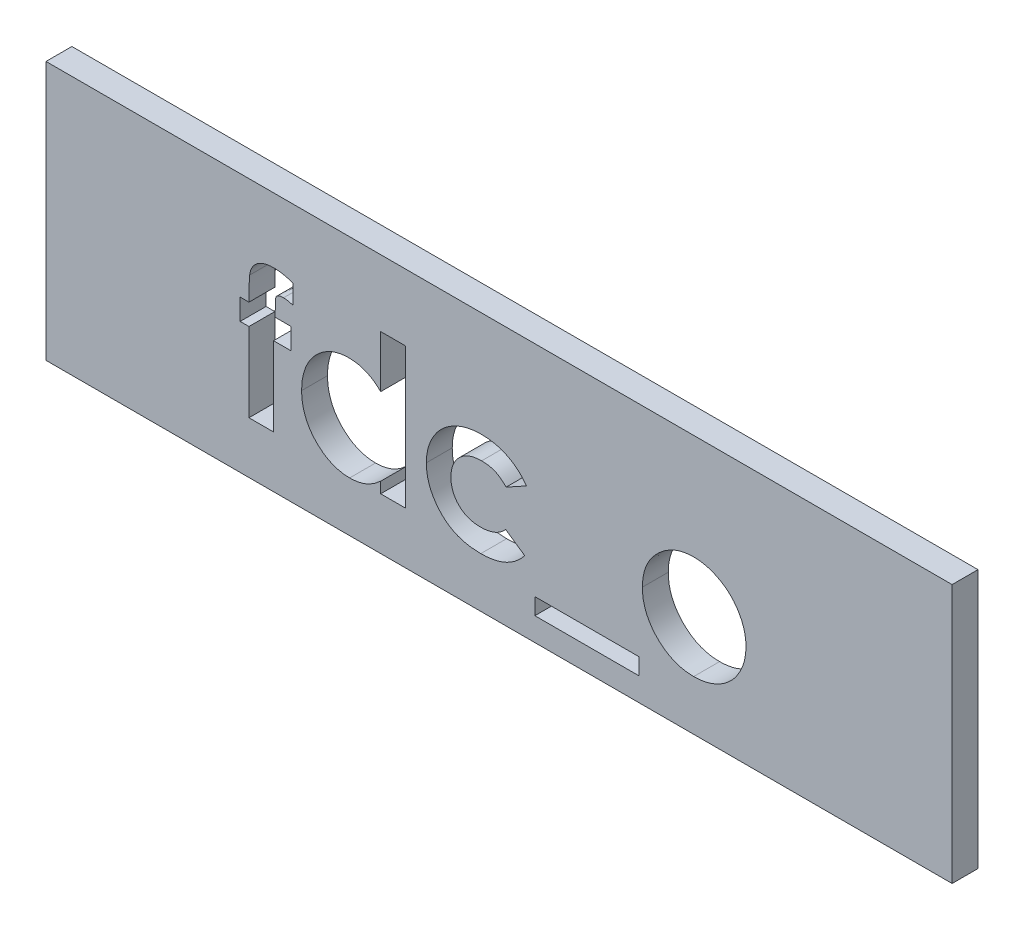
SolidWorks part; units mm, degrees
ref_plane "Plan de face" through (0, 0, 0) normal (0, 0, 1) x (1, 0, 0)
ref_plane "Plan de dessus" through (0, 0, 0) normal (0, 1, 0) x (1, 0, 0)
ref_plane "Plan de droite" through (0, 0, 0) normal (1, 0, 0) x (0, 0, -1)
sketch "Esquisse1" plane through (0, 0, 0) normal (0, 0, 1) x (1, 0, 0)
  line L1 (0, 0) -> (35, 0)
  line L2 (0, 0) -> (0, -10)
  line L3 (0, -10) -> (35, -10)
  line L4 (35, 0) -> (35, -10)
  dimension "D1" = 35
  dimension "D2" = 10
extrude "Boss.-Extru.1" add sketch "Esquisse1" along normal blind 1
sketch "Esquisse2" plane through (0, 0, 0) normal (0, 0, -1) x (-1, 0, 0)
  line L0 (-35, 0) -> (0, 0) construction
  line L1 (-35, -10) -> (-35, 0) construction
  line L2 (0, 0) -> (0, -10) construction
  circle A0 centre (-30, -5) radius 1
  circle A1 centre (-5, -5) radius 1
  dimension "D4" = 2
  dimension "D1" = 5
  dimension "D2" = 5
  dimension "D3" = 5
extrude "Boss.-Extru.2" add sketch "Esquisse2" along normal blind 3
chamfer "Chanfrein1" distance 0.5 angle 45 2 edges at (29, -5, -3) (4, -5, -3)
sketch "Esquisse3" plane through (0, 0, 1) normal (0, 0, 1) x (1, 0, 0)
  line L0 (7.5, -8) -> (27.5, -8) construction
  line L3 (0, -10) -> (35, -10) construction
  line L4 (0, 0) -> (0, -10) construction
  line L5 (35, -10) -> (35, 0) construction
  text T1 "<b>fdc_o</b>" font "Century Gothic" height in points 20
  point P12 (27.5, -8)
  dimension "D1" = 2
  dimension "D2" = 7.5
  dimension "D3" = 20
  dimension "D4" = 7.5
extrude "Enlèv. mat.-Extru.2" cut sketch "Esquisse3" against normal blind 1
sketch "Esquisse4" plane through (0, 0, 1) normal (0, 0, 1) x (1, 0, 0)
  line L8 (18.8831, -9.0998) -> (22.9144, -9.0998)
  line L9 (18.8831, -8.4606) -> (18.8831, -9.0998)
  line L10 (22.9144, -8.4606) -> (18.8831, -8.4606)
  line L11 (22.9144, -9.0998) -> (22.9144, -8.4606)
  line L12 (18.8831, -9.0998) -> (22.9144, -9.0998)
  line L13 (18.8831, -8.4606) -> (18.8831, -9.0998)
  line L14 (22.9144, -8.4606) -> (18.8831, -8.4606)
  line L15 (22.9144, -9.0998) -> (22.9144, -8.4606)
  dimension "D1" = 0.15
extrude "Enlèv. mat.-Extru.3" cut sketch "Esquisse4" against normal through all
